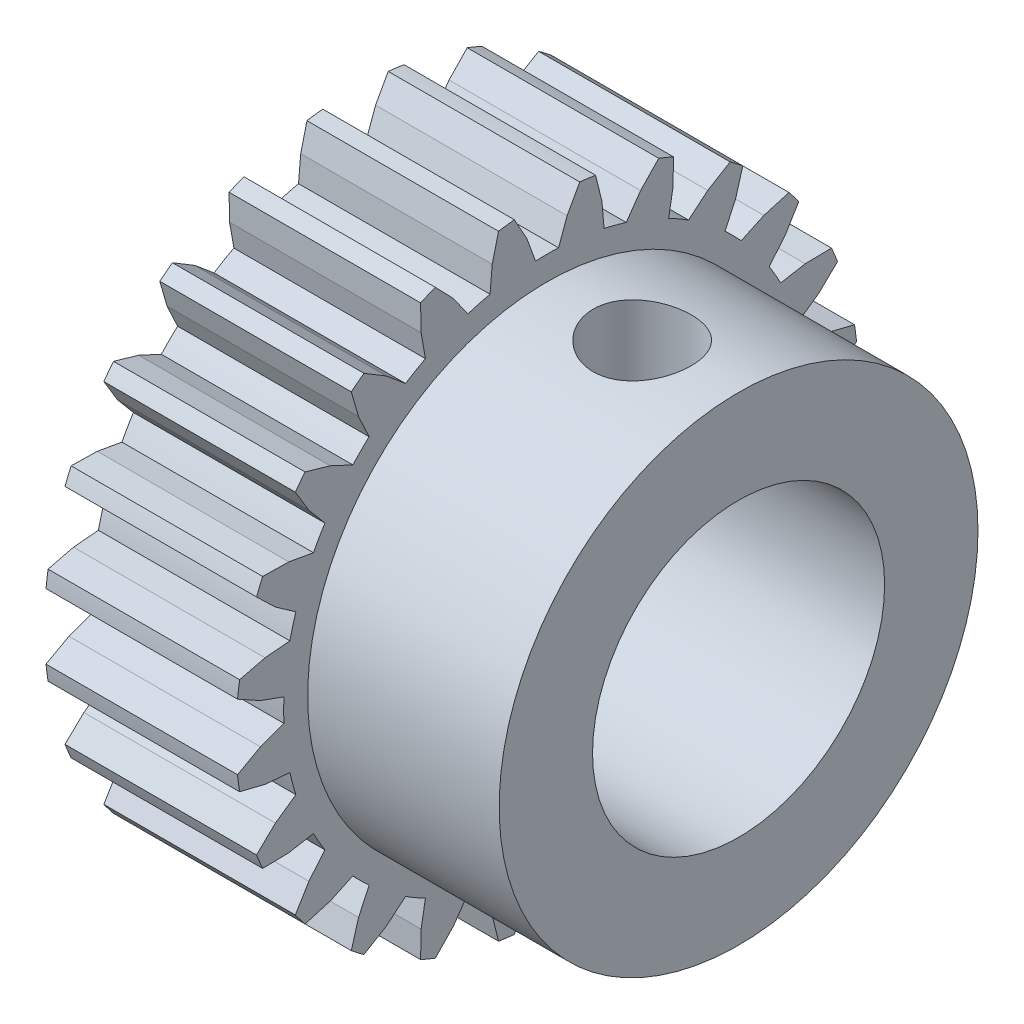
SolidWorks part; units mm, degrees
material "Plain Carbon Steel"
ref_plane "Front Plane" through (0, 0, 0) normal (0, 0, 1) x (1, 0, 0)
ref_plane "Top Plane" through (0, 0, 0) normal (0, 1, 0) x (1, 0, 0)
ref_plane "Right Plane" through (0, 0, 0) normal (1, 0, 0) x (0, 0, -1)
ref_plane "Plane1" through (2, 0, 0) normal (1, 0, 0) x (0, 0, -1)
sketch "Sketch1" plane through (2, 0, 0) normal (1, 0, 0) x (0, 0, -1)
  line L0 (-5.4948, -0.2399) -> (-5.9854, -0.4185)
  line L1 (-5.9854, -0.4185) -> (-6.464, -0.6829)
  line L2 (-6.4205, -1.0134) -> (-5.8898, -1.1449)
  line L3 (-5.8898, -1.1449) -> (-5.3696, -1.1904)
  line L4 (-5.2454, -1.6539) -> (-5.6731, -1.9534)
  line L5 (-5.6731, -1.9534) -> (-6.067, -2.3326)
  line L6 (-5.9395, -2.6406) -> (-5.3927, -2.6303)
  line L7 (-5.3927, -2.6303) -> (-4.8786, -2.5396)
  line L8 (-4.6387, -2.9551) -> (-4.9743, -3.3551)
  line L9 (-4.9743, -3.3551) -> (-5.2566, -3.8234)
  line L10 (-5.0536, -4.0879) -> (-4.5282, -3.9364)
  line L11 (-4.5282, -3.9364) -> (-4.055, -3.7157)
  line L12 (-3.7157, -4.055) -> (-3.9364, -4.5282)
  line L13 (-3.9364, -4.5282) -> (-4.0879, -5.0536)
  line L14 (-3.8234, -5.2566) -> (-3.3551, -4.9743)
  line L15 (-3.3551, -4.9743) -> (-2.9551, -4.6387)
  line L16 (-2.5396, -4.8786) -> (-2.6303, -5.3927)
  line L17 (-2.6303, -5.3927) -> (-2.6406, -5.9395)
  line L18 (-2.3326, -6.067) -> (-1.9534, -5.6731)
  line L19 (-1.9534, -5.6731) -> (-1.6539, -5.2454)
  line L20 (-1.1904, -5.3696) -> (-1.1449, -5.8898)
  line L21 (-1.1449, -5.8898) -> (-1.0134, -6.4205)
  line L22 (-0.6829, -6.464) -> (-0.4185, -5.9854)
  line L23 (-0.4185, -5.9854) -> (-0.2399, -5.4948)
  line L24 (0.2399, -5.4948) -> (0.4185, -5.9854)
  line L25 (0.4185, -5.9854) -> (0.6829, -6.464)
  line L26 (1.0134, -6.4205) -> (1.1449, -5.8898)
  line L27 (1.1449, -5.8898) -> (1.1904, -5.3696)
  line L28 (1.6539, -5.2454) -> (1.9534, -5.6731)
  line L29 (1.9534, -5.6731) -> (2.3326, -6.067)
  line L30 (2.6406, -5.9395) -> (2.6303, -5.3927)
  line L31 (2.6303, -5.3927) -> (2.5396, -4.8786)
  line L32 (2.9551, -4.6387) -> (3.3551, -4.9743)
  line L33 (3.3551, -4.9743) -> (3.8234, -5.2566)
  line L34 (4.0879, -5.0536) -> (3.9364, -4.5282)
  line L35 (3.9364, -4.5282) -> (3.7157, -4.055)
  line L36 (4.055, -3.7157) -> (4.5282, -3.9364)
  line L37 (4.5282, -3.9364) -> (5.0536, -4.0879)
  line L38 (5.2566, -3.8234) -> (4.9743, -3.3551)
  line L39 (4.9743, -3.3551) -> (4.6387, -2.9551)
  line L40 (4.8786, -2.5396) -> (5.3927, -2.6303)
  line L41 (5.3927, -2.6303) -> (5.9395, -2.6406)
  line L42 (6.067, -2.3326) -> (5.6731, -1.9534)
  line L43 (5.6731, -1.9534) -> (5.2454, -1.6539)
  line L44 (5.3696, -1.1904) -> (5.8898, -1.1449)
  line L45 (5.8898, -1.1449) -> (6.4205, -1.0134)
  line L46 (6.464, -0.6829) -> (5.9854, -0.4185)
  line L47 (5.9854, -0.4185) -> (5.4948, -0.2399)
  line L48 (5.4948, 0.2399) -> (5.9854, 0.4185)
  line L49 (5.9854, 0.4185) -> (6.464, 0.6829)
  line L50 (6.4205, 1.0134) -> (5.8898, 1.1449)
  line L51 (5.8898, 1.1449) -> (5.3696, 1.1904)
  line L52 (5.2454, 1.6539) -> (5.6731, 1.9534)
  line L53 (5.6731, 1.9534) -> (6.067, 2.3326)
  line L54 (5.9395, 2.6406) -> (5.3927, 2.6303)
  line L55 (5.3927, 2.6303) -> (4.8786, 2.5396)
  line L56 (4.6387, 2.9551) -> (4.9743, 3.3551)
  line L57 (4.9743, 3.3551) -> (5.2566, 3.8234)
  line L58 (5.0536, 4.0879) -> (4.5282, 3.9364)
  line L59 (4.5282, 3.9364) -> (4.055, 3.7157)
  line L60 (3.7157, 4.055) -> (3.9364, 4.5282)
  line L61 (3.9364, 4.5282) -> (4.0879, 5.0536)
  line L62 (3.8234, 5.2566) -> (3.3551, 4.9743)
  line L63 (3.3551, 4.9743) -> (2.9551, 4.6387)
  line L64 (2.5396, 4.8786) -> (2.6303, 5.3927)
  line L65 (2.6303, 5.3927) -> (2.6406, 5.9395)
  line L66 (2.3326, 6.067) -> (1.9534, 5.6731)
  line L67 (1.9534, 5.6731) -> (1.6539, 5.2454)
  line L68 (1.1904, 5.3696) -> (1.1449, 5.8898)
  line L69 (1.1449, 5.8898) -> (1.0134, 6.4205)
  line L70 (0.6829, 6.464) -> (0.4185, 5.9854)
  line L71 (0.4185, 5.9854) -> (0.2399, 5.4948)
  line L72 (-0.2399, 5.4948) -> (-0.4185, 5.9854)
  line L73 (-0.4185, 5.9854) -> (-0.6829, 6.464)
  line L74 (-1.0134, 6.4205) -> (-1.1449, 5.8898)
  line L75 (-1.1449, 5.8898) -> (-1.1904, 5.3696)
  line L76 (-1.6539, 5.2454) -> (-1.9534, 5.6731)
  line L77 (-1.9534, 5.6731) -> (-2.3326, 6.067)
  line L78 (-2.6406, 5.9395) -> (-2.6303, 5.3927)
  line L79 (-2.6303, 5.3927) -> (-2.5396, 4.8786)
  line L80 (-2.9551, 4.6387) -> (-3.3551, 4.9743)
  line L81 (-3.3551, 4.9743) -> (-3.8234, 5.2566)
  line L82 (-4.0879, 5.0536) -> (-3.9364, 4.5282)
  line L83 (-3.9364, 4.5282) -> (-3.7157, 4.055)
  line L84 (-4.055, 3.7157) -> (-4.5282, 3.9364)
  line L85 (-4.5282, 3.9364) -> (-5.0536, 4.0879)
  line L86 (-5.2566, 3.8234) -> (-4.9743, 3.3551)
  line L87 (-4.9743, 3.3551) -> (-4.6387, 2.9551)
  line L88 (-4.8786, 2.5396) -> (-5.3927, 2.6303)
  line L89 (-5.3927, 2.6303) -> (-5.9395, 2.6406)
  line L90 (-6.067, 2.3326) -> (-5.6731, 1.9534)
  line L91 (-5.6731, 1.9534) -> (-5.2454, 1.6539)
  line L92 (-5.3696, 1.1904) -> (-5.8898, 1.1449)
  line L93 (-5.8898, 1.1449) -> (-6.4205, 1.0134)
  line L94 (-6.464, 0.6829) -> (-5.9854, 0.4185)
  line L95 (-5.9854, 0.4185) -> (-5.4948, 0.2399)
  arc A0 (-6.464, -0.6829) -> (-6.4205, -1.0134) centre (0, 0) ccw
  arc A1 (-5.3696, -1.1904) -> (-5.2454, -1.6539) centre (0, 0) ccw
  arc A2 (-6.067, -2.3326) -> (-5.9395, -2.6406) centre (0, 0) ccw
  arc A3 (-4.8786, -2.5396) -> (-4.6387, -2.9551) centre (0, 0) ccw
  arc A4 (-5.2566, -3.8234) -> (-5.0536, -4.0879) centre (0, 0) ccw
  arc A5 (-4.055, -3.7157) -> (-3.7157, -4.055) centre (0, 0) ccw
  arc A6 (-4.0879, -5.0536) -> (-3.8234, -5.2566) centre (0, 0) ccw
  arc A7 (-2.9551, -4.6387) -> (-2.5396, -4.8786) centre (0, 0) ccw
  arc A8 (-2.6406, -5.9395) -> (-2.3326, -6.067) centre (0, 0) ccw
  arc A9 (-1.6539, -5.2454) -> (-1.1904, -5.3696) centre (0, 0) ccw
  arc A10 (-1.0134, -6.4205) -> (-0.6829, -6.464) centre (0, 0) ccw
  arc A11 (-0.2399, -5.4948) -> (0.2399, -5.4948) centre (0, 0) ccw
  arc A12 (0.6829, -6.464) -> (1.0134, -6.4205) centre (0, 0) ccw
  arc A13 (1.1904, -5.3696) -> (1.6539, -5.2454) centre (0, 0) ccw
  arc A14 (2.3326, -6.067) -> (2.6406, -5.9395) centre (0, 0) ccw
  arc A15 (2.5396, -4.8786) -> (2.9551, -4.6387) centre (0, 0) ccw
  arc A16 (3.8234, -5.2566) -> (4.0879, -5.0536) centre (0, 0) ccw
  arc A17 (3.7157, -4.055) -> (4.055, -3.7157) centre (0, 0) ccw
  arc A18 (5.0536, -4.0879) -> (5.2566, -3.8234) centre (0, 0) ccw
  arc A19 (4.6387, -2.9551) -> (4.8786, -2.5396) centre (0, 0) ccw
  arc A20 (5.9395, -2.6406) -> (6.067, -2.3326) centre (0, 0) ccw
  arc A21 (5.2454, -1.6539) -> (5.3696, -1.1904) centre (0, 0) ccw
  arc A22 (6.4205, -1.0134) -> (6.464, -0.6829) centre (0, 0) ccw
  arc A23 (5.4948, -0.2399) -> (5.4948, 0.2399) centre (0, 0) ccw
  arc A24 (6.464, 0.6829) -> (6.4205, 1.0134) centre (0, 0) ccw
  arc A25 (5.3696, 1.1904) -> (5.2454, 1.6539) centre (0, 0) ccw
  arc A26 (6.067, 2.3326) -> (5.9395, 2.6406) centre (0, 0) ccw
  arc A27 (4.8786, 2.5396) -> (4.6387, 2.9551) centre (0, 0) ccw
  arc A28 (5.2566, 3.8234) -> (5.0536, 4.0879) centre (0, 0) ccw
  arc A29 (4.055, 3.7157) -> (3.7157, 4.055) centre (0, 0) ccw
  arc A30 (4.0879, 5.0536) -> (3.8234, 5.2566) centre (0, 0) ccw
  arc A31 (2.9551, 4.6387) -> (2.5396, 4.8786) centre (0, 0) ccw
  arc A32 (2.6406, 5.9395) -> (2.3326, 6.067) centre (0, 0) ccw
  arc A33 (1.6539, 5.2454) -> (1.1904, 5.3696) centre (0, 0) ccw
  arc A34 (1.0134, 6.4205) -> (0.6829, 6.464) centre (0, 0) ccw
  arc A35 (0.2399, 5.4948) -> (-0.2399, 5.4948) centre (0, 0) ccw
  arc A36 (-0.6829, 6.464) -> (-1.0134, 6.4205) centre (0, 0) ccw
  arc A37 (-1.1904, 5.3696) -> (-1.6539, 5.2454) centre (0, 0) ccw
  arc A38 (-2.3326, 6.067) -> (-2.6406, 5.9395) centre (0, 0) ccw
  arc A39 (-2.5396, 4.8786) -> (-2.9551, 4.6387) centre (0, 0) ccw
  arc A40 (-3.8234, 5.2566) -> (-4.0879, 5.0536) centre (0, 0) ccw
  arc A41 (-3.7157, 4.055) -> (-4.055, 3.7157) centre (0, 0) ccw
  arc A42 (-5.0536, 4.0879) -> (-5.2566, 3.8234) centre (0, 0) ccw
  arc A43 (-4.6387, 2.9551) -> (-4.8786, 2.5396) centre (0, 0) ccw
  arc A44 (-5.9395, 2.6406) -> (-6.067, 2.3326) centre (0, 0) ccw
  arc A45 (-5.2454, 1.6539) -> (-5.3696, 1.1904) centre (0, 0) ccw
  arc A46 (-6.4205, 1.0134) -> (-6.464, 0.6829) centre (0, 0) ccw
  arc A47 (-5.4948, 0.2399) -> (-5.4948, -0.2399) centre (0, 0) ccw
extrude "Boss-Extrude1" add sketch "Sketch1" against normal blind 4
sketch "Sketch2" plane through (0, 0, 0) normal (0, 0, 1) x (1, 0, 0)
  line L0 (2, 5) -> (2, 0)
  line L1 (2, 0) -> (6, 0)
  line L2 (6, 0) -> (6, 5)
  line L3 (6, 5) -> (2, 5)
  line L4 (2, 0) -> (6, 0) construction
revolve "Revolve1" add sketch "Sketch2" angle 360 about L4
hole_wizard "Ø6.1 (6.1) Diameter Hole1" positions "Sketch4" profile "Sketch3" hole size "Ø6.1" standard "ANSI Metric"
sketch "Sketch4" plane through (6, 0, 0) normal (1, 0, 0) x (0, 0, -1)
  point P0 (0, 0)
sketch "Sketch3" plane through (6, 0, 0) normal (0, 1, 0) x (0, 0, -1)
  line L0 (0, 0) -> (0, 8)
  line L1 (0, 8) -> (3.05, 8)
  line L2 (3.05, 8) -> (3.05, 0)
  line L5 (3.05, 0) -> (0, 0)
  line L11 (0, -6.35) -> (0, 107.95) construction
  dimension "Thru Hole Dia." = 6.1
  dimension "Thru Hole Depth" = 8
ref_plane "Plane2" through (0, 2.8726, 0.0075) normal (0, -1, -0.0026) x (-1, 0, 0)
hole_wizard "Ø2.05 (2.05) Diameter Hole1" positions "Sketch6" profile "Sketch5" hole size "Ø2.05" standard "ANSI Metric"
sketch "Sketch6" plane through (0, 2.8726, 0.0075) normal (0, -1, -0.0026) x (-1, 0, 0)
  point P0 (-4, 0)
sketch "Sketch5" plane through (4, 2.8726, 0.0075) normal (1, 0, 0) x (0, 0.0026, -1)
  line L0 (0, 0) -> (0, 10)
  line L1 (0, 10) -> (1.025, 10)
  line L2 (1.025, 10) -> (1.025, 0)
  line L5 (1.025, 0) -> (0, 0)
  line L10 (0, 10) -> (-1.025, 10) construction
  line L11 (0, -6.35) -> (0, 107.95) construction
  dimension "Hole Dia." = 2.05
  dimension "Hole Depth" = 10
  dimension "Drill Angle" = 180
